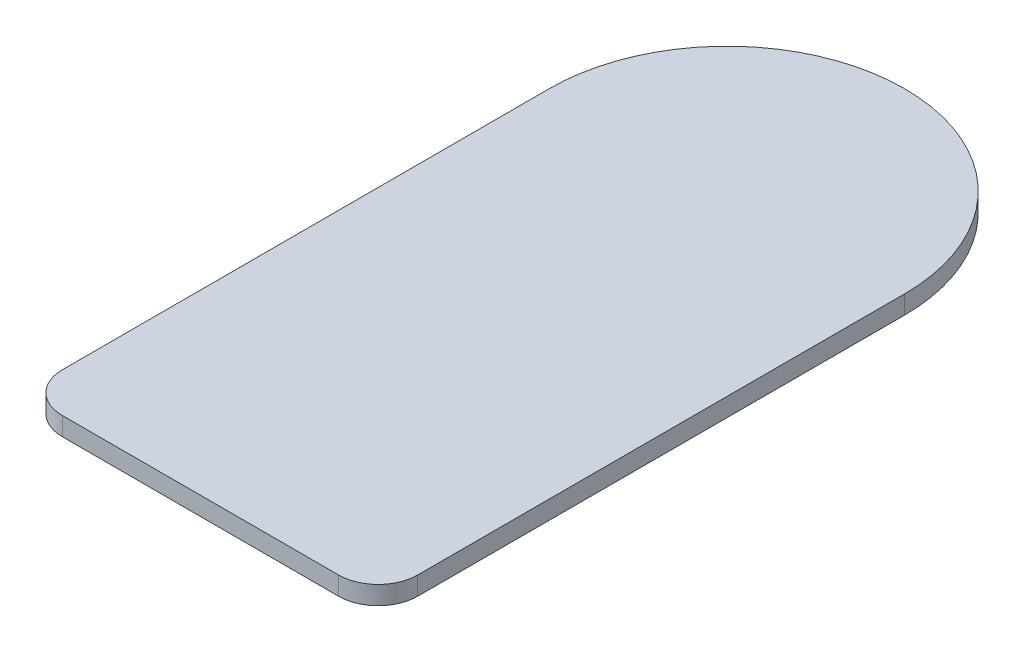
SolidWorks part; units mm, degrees
ref_plane "Front Plane" through (0, 0, 0) normal (0, 0, 1) x (1, 0, 0)
ref_plane "Top Plane" through (0, 0, 0) normal (0, 1, 0) x (1, 0, 0)
ref_plane "Right Plane" through (0, 0, 0) normal (1, 0, 0) x (0, 0, -1)
sketch "Sketch1" plane through (0, 0, 0) normal (0, 1, 0) x (1, 0, 0)
  line L0 (0, 0) -> (0, 100) construction
  line L1 (52.5, -100) -> (-52.5, -100)
  line L2 (67.5, -85) -> (67.5, 100)
  line L4 (-67.5, -85) -> (-67.5, 100)
  line L5 (67.5, -100) -> (-67.5, 100) construction
  line L6 (67.5, 100) -> (-67.5, -100) construction
  arc A0 (67.5, 100) -> (-67.5, 100) centre (0, 100) ccw
  arc A1 (52.5, -100) -> (67.5, -85) centre (52.5, -85) ccw
  arc A2 (-52.5, -100) -> (-67.5, -85) centre (-52.5, -85) cw
  point P0 (0, 0)
  dimension "D3" = 15
  dimension "D1" = 200
  dimension "D2" = 135
extrude "Boss-Extrude1" add sketch "Sketch1" along normal blind 7 contours L4 A0 L2 A1 L1 A2
